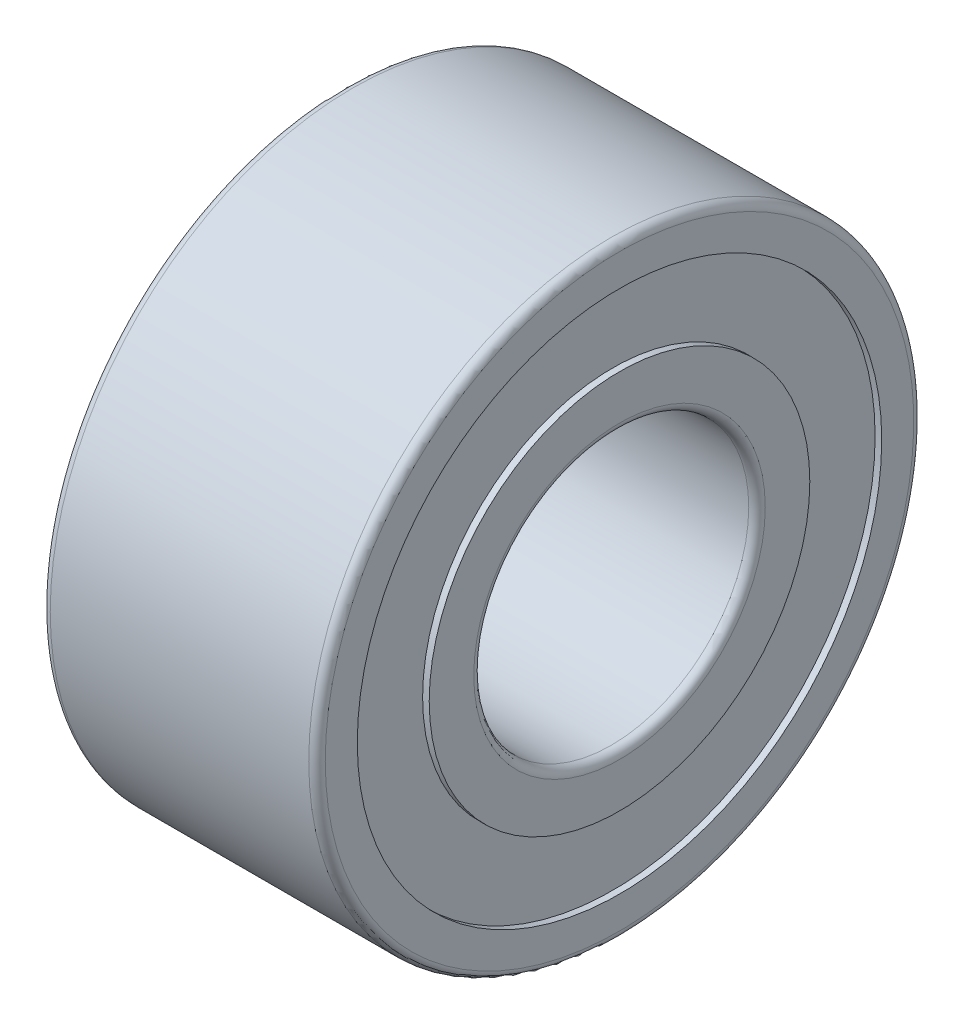
SolidWorks part; units mm, degrees
ref_plane "Front Plane" through (0, 0, 0) normal (0, 0, 1) x (1, 0, 0)
ref_plane "Top Plane" through (0, 0, 0) normal (0, 1, 0) x (1, 0, 0)
ref_plane "Right Plane" through (0, 0, 0) normal (1, 0, 0) x (0, 0, -1)
sketch "Sketch1" plane through (0, 0, 0) normal (0, 0, 1) x (1, 0, 0)
  line L0 (0, 0) -> (5, 0) construction
  line L1 (0, 2.5) -> (5, 2.5)
  line L2 (0, 5.5) -> (5, 5.5)
  line L3 (0, 5.5) -> (0, 4.7675)
  line L4 (0, 4.7675) -> (0.12, 4.7675)
  line L5 (5, 5.5) -> (5, 4.7675)
  line L6 (0.12, 4.7675) -> (0.12, 3.46)
  line L7 (0.12, 3.46) -> (0, 3.46)
  line L8 (0, 3.46) -> (0, 2.5)
  line L9 (5, 4.7675) -> (4.88, 4.7675)
  line L10 (4.88, 4.7675) -> (4.88, 3.46)
  line L11 (4.88, 3.46) -> (5, 3.46)
  line L12 (5, 3.46) -> (5, 2.5)
  dimension "D" = 11
  dimension "B" = 5
  dimension "D_s" = 5
  dimension "MSM_1" = 9.535
  dimension "MSM_2" = 6.92
  dimension "MSM_3" = 0.12
revolve "Revolve1" add sketch "Sketch1" angle 360 about L0
fillet "Fillet1" radius 0.15 2 edges at (5, 0, 5.5) (0, 0, 5.5)
fillet "Fillet2" radius 0.15 2 edges at (5, 0, 2.5) (0, 0, 2.5)
ref_plane "Plane1" through (2.5, 0, 0) normal (1, 0, 0) x (0, 0, -1)
